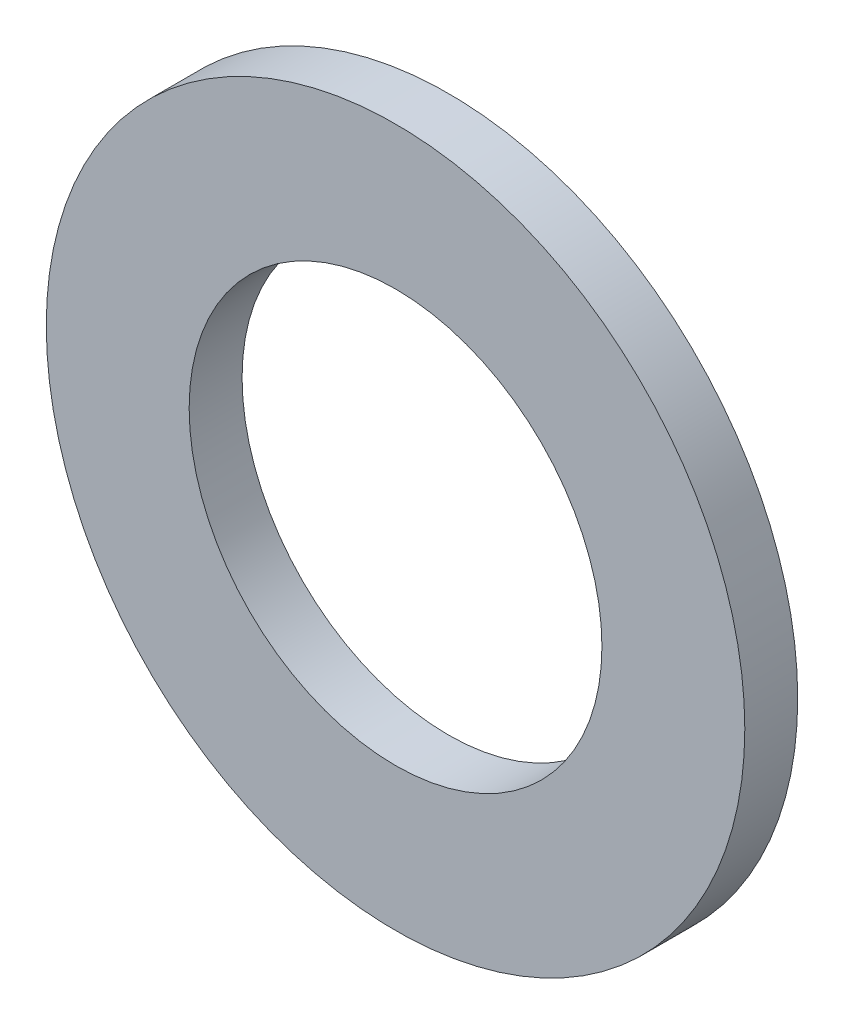
SolidWorks part; units mm, degrees
material "Резина"
ref_plane "Спереди" through (0, 0, 0) normal (0, 0, 1) x (1, 0, 0)
ref_plane "Сверху" through (0, 0, 0) normal (0, 1, 0) x (1, 0, 0)
ref_plane "Справа" through (0, 0, 0) normal (1, 0, 0) x (0, 0, -1)
sketch "Эскиз1" plane through (0, 0, 0) normal (0, 0, 1) x (1, 0, 0)
  circle A0 centre (0, 0) radius 19.5
  circle A1 centre (0, 0) radius 33
  dimension "D1" = 66
  dimension "D2" = 39
extrude "Бобышка-Вытянуть1" add sketch "Эскиз1" along normal blind 5
